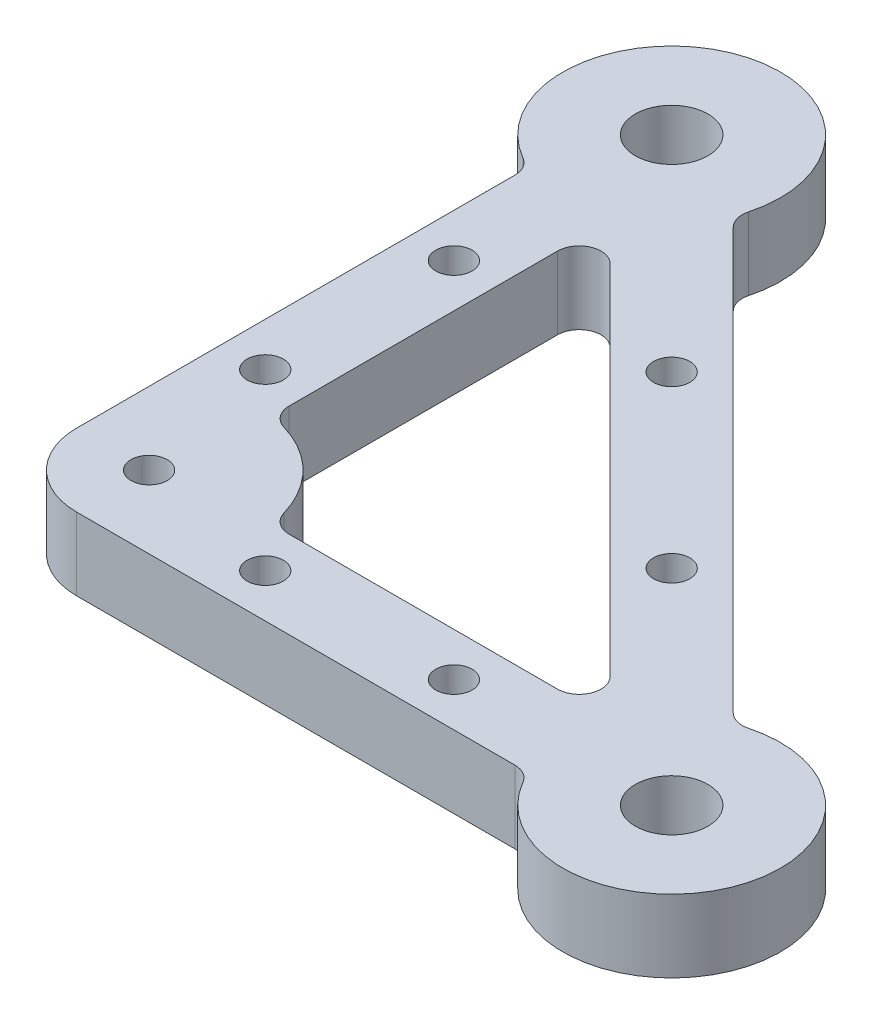
SolidWorks part; units mm, degrees
ref_plane "Front Plane" through (0, 0, 0) normal (0, 0, 1) x (1, 0, 0)
ref_plane "Top Plane" through (0, 0, 0) normal (0, 1, 0) x (1, 0, 0)
ref_plane "Right Plane" through (0, 0, 0) normal (1, 0, 0) x (0, 0, -1)
sketch "Sketch2" plane through (0, 0, 0) normal (0, 1, 0) x (1, 0, 0)
  line L0 (0, 0) -> (0, -86) construction
  line L1 (80, -80) -> (-6, -80) construction
  line L3 (66.2523, -86) -> (-6, -86)
  line L5 (-6, -86) -> (-6, -13.7477)
  line L6 (0, 0) -> (80, -80) construction
  line L7 (65.5147, -74) -> (18.8661, -74)
  line L8 (6, -61.1339) -> (6, -14.4853)
  line L9 (6, -14.4853) -> (65.5147, -74)
  line L12 (13.9638, -5.4785) -> (74.5215, -66.0362)
  arc A0 (13.9638, -5.4785) -> (-6, -13.7477) centre (0, 0) ccw
  arc A1 (66.2523, -86) -> (74.5215, -66.0362) centre (80, -80) ccw
  circle A2 centre (0, 0) radius 5
  circle A3 centre (80, -80) radius 5
  circle A4 centre (50, -80) radius 2.5
  circle A5 centre (24, -80) radius 2.5
  circle A6 centre (0, -56) radius 2.5
  circle A7 centre (0, -30) radius 2.5
  circle A8 centre (28.2843, -28.2843) radius 2.5
  circle A9 centre (51.7157, -51.7157) radius 2.5
  circle A10 centre (4, -76) radius 2.5
  arc A11 (18.8661, -74) -> (6, -61.1339) centre (4, -76) ccw
  dimension "D1" = 30
  dimension "D2" = 30
  dimension "D8" = 10
  dimension "D9" = 10
  dimension "D10" = 5
  dimension "D11" = 5
  dimension "D12" = 5
  dimension "D13" = 5
  dimension "D14" = 5
  dimension "D15" = 5
  dimension "D22" = 5
  dimension "D28" = 30
  dimension "D3" = 80
  dimension "D4" = 80
  dimension "D5" = 6
  dimension "D6" = 6
  dimension "D7" = 6
  dimension "D16" = 30
  dimension "D17" = 26
  dimension "D18" = 40
  dimension "D19" = 40
  dimension "D20" = 30
  dimension "D21" = 26
  dimension "D23" = 20
  dimension "D24" = 4
  dimension "D25" = 6
  dimension "D26" = 6
  dimension "D27" = 6
extrude "Boss-Extrude1" add sketch "Sketch2" along normal blind 10
fillet "Fillet1" radius 10 1 edges at (-6, 5, 86)
fillet "Fillet2" radius 3 4 edges at (74.5215, 5, 66.0362) (13.9638, 5, 5.4785) (-6, 5, 13.7477) (66.2523, 5, 86)
fillet "Fillet3" radius 3 2 edges at (65.5147, 5, 74) (6, 5, 14.4853)
fillet "Fillet4" radius 3 2 edges at (18.8661, 5, 74) (6, 5, 61.1339)
